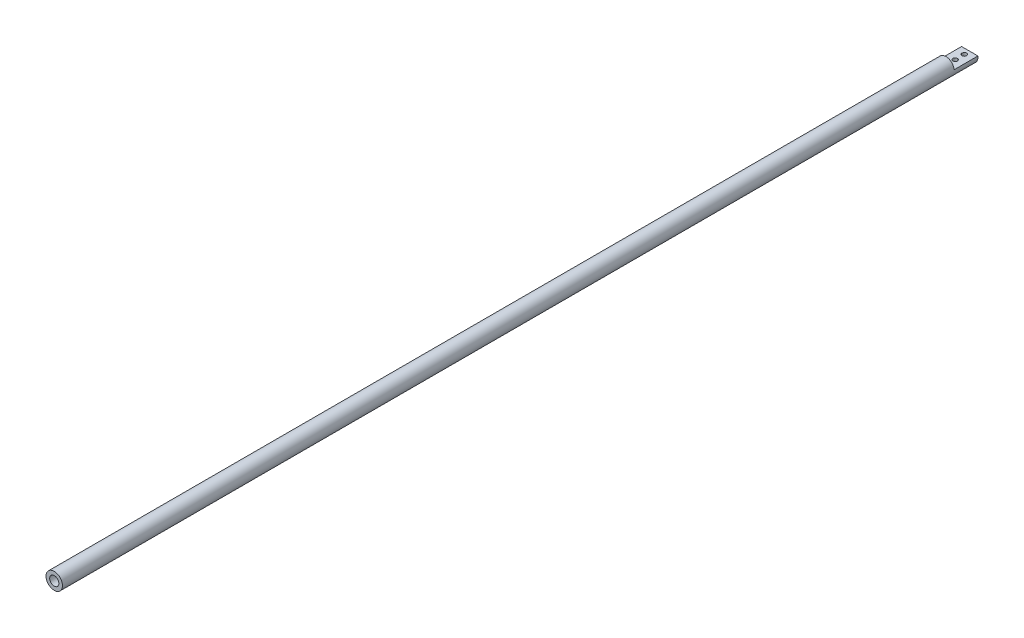
SolidWorks part; units mm, degrees
ref_plane "Alzado" through (0, 0, 0) normal (0, 0, 1) x (1, 0, 0)
ref_plane "Planta" through (0, 0, 0) normal (0, 1, 0) x (1, 0, 0)
ref_plane "Vista lateral" through (0, 0, 0) normal (1, 0, 0) x (0, 0, -1)
sketch "Croquis1" plane through (0, 0, 0) normal (0, 0, 1) x (1, 0, 0)
  circle A0 centre (0, 0) radius 9
extrude "Saliente-Extruir1" add sketch "Croquis1" along normal blind 1000
sketch "Croquis2" plane through (0, 0, 1000) normal (0, 0, 1) x (1, 0, 0)
  circle A0 centre (0, 0) radius 5
extrude "Cortar-Extruir1" cut sketch "Croquis2" against normal blind 30
sketch "Croquis4" plane through (0, 0, 0) normal (0, 0, -1) x (-1, 0, 0)
  line L4 (-8.9443, 1) -> (8.9443, 1)
  arc A1 (8.9443, 1) -> (0, 9) centre (0, 0) ccw
  circle A2 centre (0, 0) radius 9 construction
  arc A3 (0, 9) -> (-8.9443, 1) centre (0, 0) ccw
  point P4 (0, 0)
extrude "Cortar-Extruir2" cut sketch "Croquis4" against normal blind 26
sketch "Croquis5" plane through (0, 1, 0) normal (0, 1, 0) x (1, 0, 0)
  line L0 (0, 0) -> (0, -6) construction
  line L1 (0, -6) -> (0, -16) construction
  circle A0 centre (0, -6) radius 2.5
  circle A1 centre (0, -16) radius 2.5
  dimension "D2" = 10
  dimension "D1" = 6
extrude "Cortar-Extruir3" cut sketch "Croquis5" against normal blind 10
